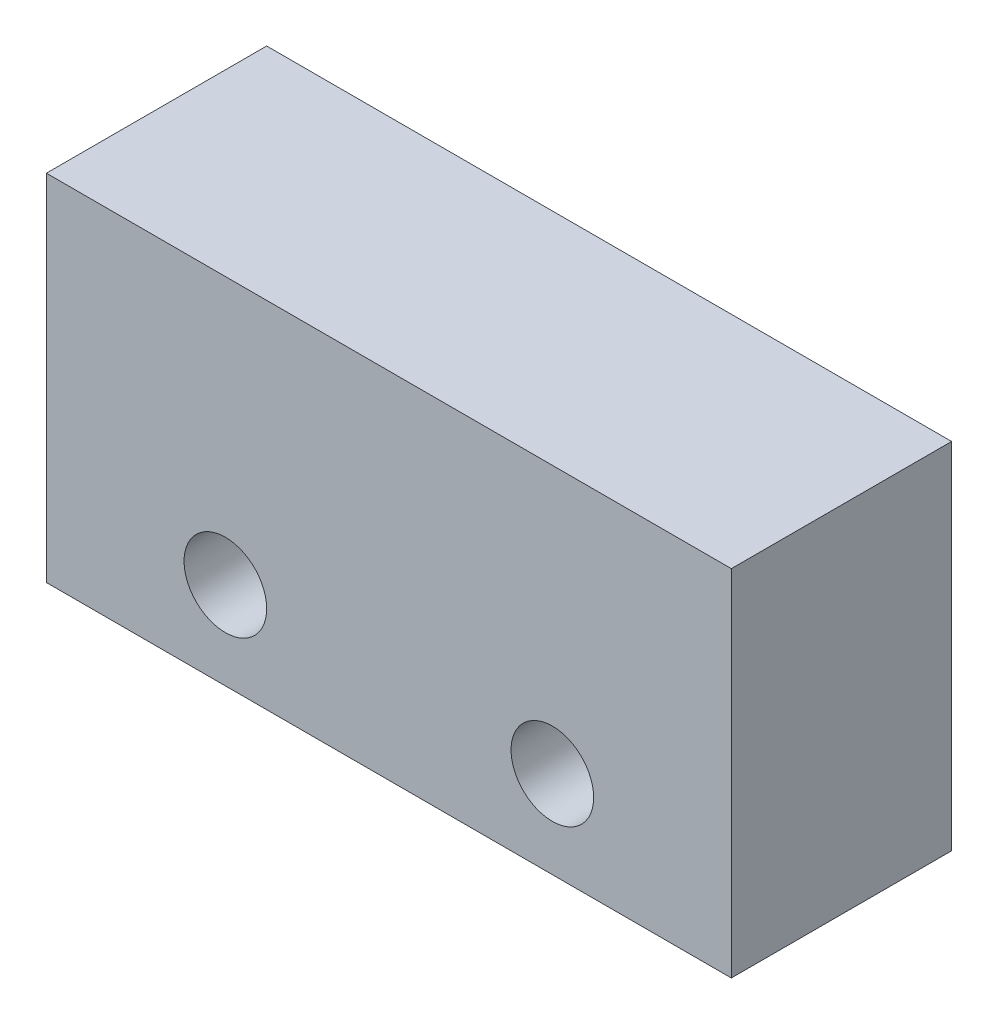
SolidWorks part; units mm, degrees
ref_plane "Front Plane" through (0, 0, 0) normal (0, 0, 1) x (1, 0, 0)
ref_plane "Top Plane" through (0, 0, 0) normal (0, 1, 0) x (1, 0, 0)
ref_plane "Right Plane" through (0, 0, 0) normal (1, 0, 0) x (0, 0, -1)
sketch "Sketch1" plane through (0, 0, 0) normal (0, 0, 1) x (1, 0, 0)
  line L1 (9.95, -5.15) -> (-9.95, -5.15)
  line L2 (9.95, -5.15) -> (9.95, 5.15)
  line L3 (9.95, 5.15) -> (-9.95, 5.15)
  line L4 (-9.95, -5.15) -> (-9.95, 5.15)
  line L5 (9.95, -5.15) -> (-9.95, 5.15) construction
  line L6 (9.95, 5.15) -> (-9.95, -5.15) construction
  circle A0 centre (-4.75, -2.61) radius 1.2
  circle A1 centre (4.75, -2.61) radius 1.2
  point P0 (0, 0)
  dimension "D3" = 2.4
  dimension "D4" = 2.4
  dimension "D1" = 19.9
  dimension "D2" = 10.3
  dimension "D5" = 9.5
  dimension "D6" = 5.2
  dimension "D7" = 2.54
extrude "Boss-Extrude1" add sketch "Sketch1" along normal blind 6.4
